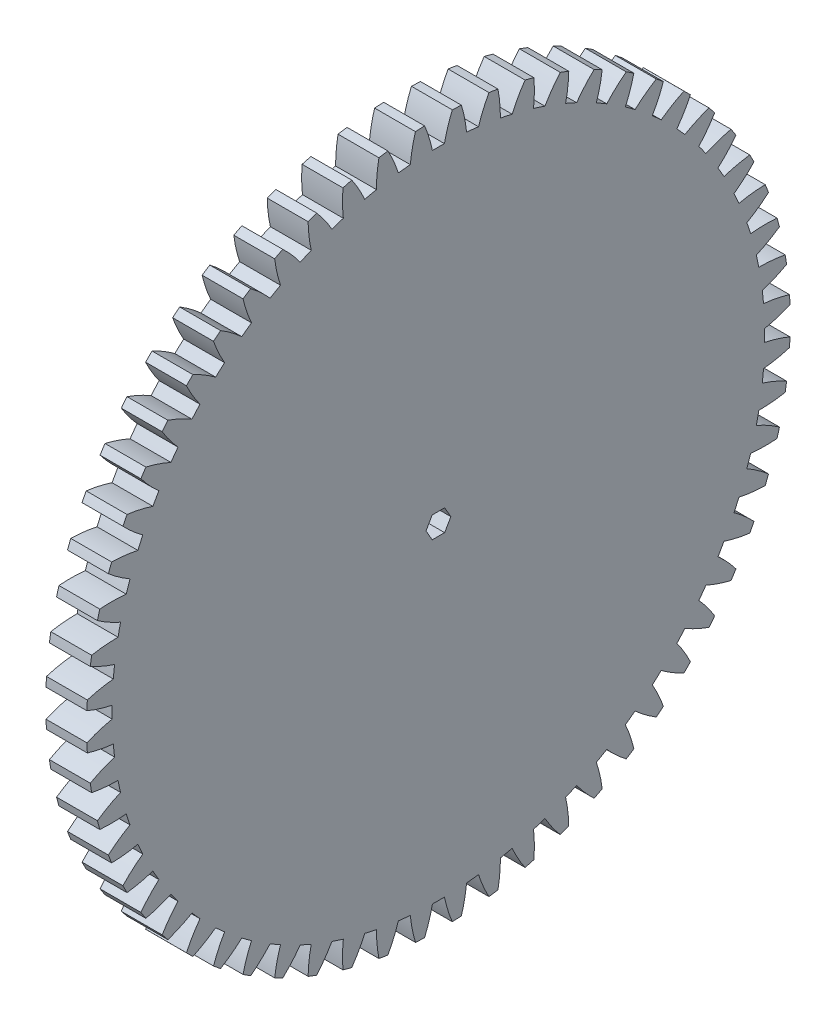
SolidWorks part; units mm, degrees
ref_plane "Plane1" through (0, 0, 0) normal (0, 0, 1) x (1, 0, 0)
ref_plane "Plane2" through (0, 0, 0) normal (0, 1, 0) x (1, 0, 0)
ref_plane "Plane3" through (0, 0, 0) normal (1, 0, 0) x (0, 0, -1)
sketch "HoldingSke" plane through (0, 0, 0) normal (0, 1, 0) x (1, 0, 0)
  line L0 (0, 0) -> (304.8, -527.9291)
  line L1 (-15, 0) -> (100, 0) construction
  line L2 (0, 0) -> (-2.1039, 2.3779)
  line L3 (0, 0) -> (-11.863, 4.5341)
  line L4 (0, 0) -> (4.318, 7.479)
  line L5 (0, 0) -> (-47.5972, -17.7524)
  line L6 (0, 0) -> (-3.1583, -2.1309)
  line L7 (-2.1039, 2.3779) -> (8.8308, 51.9871)
  line L8 (-76.2, 54.61) -> (-61.976, 54.61)
  line L9 (-67.7845, 28.3722) -> (-49.3413, 33.142)
  line L10 (-76.2, 71.12) -> (104.1128, 71.12)
  line L11 (0, 0) -> (-3.81, 0)
  line L12 (-76.2, 101.6) -> (-76.1573, 101.6)
  line L13 (24.9733, 27.94) -> (52.9518, 28.4284)
  line L14 (24.9733, 27.94) -> (25.0241, 27.9398)
  line L15 (24.9733, 27.94) -> (100.4021, 29.52)
  circle A0 centre (0, 0) radius 6.35
  circle A1 centre (0, 0) radius 30.4292
  circle A2 centre (0, 0) radius 38.1
  circle A3 centre (0, 0) radius 6.35
  dimension "MHD" = 60.8584
  dimension "Hub_dia" = 76.2
  dimension "Bore" = 12.7
  dimension "MBD" = 12.7
  dimension "Num_teeth" = 60
  dimension "Pitch" = 609.6
  dimension "Overall_len" = 50.8
  dimension "Show_teeth" = 60
  dimension "Thickness" = 3.81
  dimension "OAL" = 50.8001
  dimension "T_dim" = 14.224
  dimension "Ap" = 14.5
  dimension "H" = 19.05
  dimension "Pitch_radius" = 180.3128
  dimension "Width" = 3.81
  dimension "Backlash" = 0.0427
  dimension "Addendum_fac" = 1
  dimension "Dedendum_fac" = 1.2
  dimension "Clearance_fac" = 0.2
  dimension "Dedendum_add" = 0.0508
sketch "BasProSke" plane through (0, 0, 0) normal (0, 1, 0) x (1, 0, 0)
  line L0 (-10, 0) -> (60, 0) construction
  line L1 (0, 0) -> (0, 32.8083)
  line L2 (0, 0) -> (3.81, 0)
  line L3 (3.81, 0) -> (3.81, 32.8083)
  line L4 (3.81, 32.8083) -> (0, 32.8083)
  dimension "Thickness" = 3.81
  dimension "Diameter" = 65.6167
revolve "Base-Revolve" add sketch "BasProSke" angle 360 about L0
sketch "TooCutSke" plane through (0, 0, 0) normal (1, 0, 0) x (0, 0, -1)
  line L1 (0, 0) -> (0, 107) construction
  line L2 (0, 0) -> (-0.9058, 31.7371) construction
  line L3 (0, 0) -> (-3.3224, 63.395) construction
  line L4 (-0.9058, 31.7371) -> (-1.6612, 31.6975) construction
  arc A0 (0.5605, 30.424) -> (-0.5605, 30.424) centre (0, 0) ccw
  arc A1 (1.3035, 32.8078) -> (-1.3035, 32.8078) centre (0, 0) ccw
  circle A2 centre (0, 0) radius 31.75 construction
  circle A3 centre (0, 0) radius 30.7387 construction
  arc A4 (-0.5605, 30.424) -> (-1.3035, 32.8078) centre (-12.998, 27.8553) ccw
  arc A5 (1.3035, 32.8078) -> (0.5605, 30.424) centre (12.998, 27.8553) ccw
  dimension "Root_dia" = 60.8584
  dimension "Overcut_dia" = 65.6675
  dimension "Pitch_dia" = 63.5
  dimension "Base_dia" = 61.4774
  dimension "Flank_rad" = 12.7
  dimension "Half_ang" = 3
  dimension "Half_CT" = 0.7564
extrude "ToothCut" cut sketch "TooCutSke" along normal through all
fillet "Breaks" [suppressed] radius 0.0212
fillet "RootFillets" [suppressed] radius 0.2625
pattern_circular "TeethCuts" count 60 every 6 about axis through (-10, 0, 0) along (1, 0, 0) of "ToothCut", "RootFillets", "Breaks"
sketch "HubNeaOneSke" plane through (0, 0, 0) normal (-1, 0, 0) x (0, 0, 1)
  circle A0 centre (0, 0) radius 30.4292
  dimension "Diameter" = 60.8584
extrude "HubNearOne" [suppressed] add sketch "HubNeaOneSke" along normal blind 46.9901
sketch "HubNeaBotSke" plane through (0, 0, 0) normal (-1, 0, 0) x (0, 0, 1)
  circle A0 centre (0, 0) radius 30.4292
  dimension "Diameter" = 60.8584
extrude "HubNearBoth" [suppressed] add sketch "HubNeaBotSke" along normal blind 23.495
ref_plane "FarPln" through (3.81, 0, 0) normal (1, 0, 0) x (0, 0, -1)
sketch "HubFarSke" plane through (3.81, 0, 0) normal (1, 0, 0) x (0, 0, -1)
  circle A0 centre (0, 0) radius 30.4292
  dimension "Diameter" = 60.8584
extrude "HubFar" [suppressed] add sketch "HubFarSke" along normal blind 23.495
sketch "BorSke" plane through (0, 0, 0) normal (1, 0, 0) x (0, 0, -1)
  circle A0 centre (0, 0) radius 6.35
  dimension "Diameter" = 12.7
extrude "Bore" cut sketch "BorSke" along normal mid plane 101.6001
sketch "KeySke" plane through (0, 0, 0) normal (1, 0, 0) x (0, 0, -1)
  line L0 (-1.5875, 0) -> (-1.5875, 7.874)
  line L1 (-1.5875, 7.874) -> (1.5875, 7.874)
  line L2 (1.5875, 7.874) -> (1.5875, 0)
  line L3 (0, 0) -> (0, 34) construction
  line L4 (-1.5875, 0) -> (1.5875, 0)
  dimension "Offset" = 7.874
  dimension "Width" = 3.175
extrude "Keyway" [suppressed] cut sketch "KeySke" along normal mid plane 101.6001
pattern_circular "Keyway2" [suppressed] count 2 every 90 about axis through (-10, 0, 0) along (1, 0, 0)
sketch "Sketch1" plane through (3.81, 0, 0) normal (1, 0, 0) x (0, 0, -1)
  circle A0 centre (0, 0) radius 6.35 construction
  circle A1 centre (0, 0) radius 6.35
extrude "Boss-Extrude1" add sketch "Sketch1" against normal blind 7.62
sketch "Sketch2" plane through (-3.81, 0, 0) normal (-1, 0, 0) x (0, 0, 1)
  line L0 (0, 0) -> (7.1354, 0) construction
  line L1 (0, 0) -> (0, 8.2626) construction
  line L3 (1.1585, 0) -> (0.5793, 1.0033)
  line L4 (0.5793, 1.0033) -> (-0.5793, 1.0033)
  line L5 (-0.5793, 1.0033) -> (-1.1585, 0)
  line L6 (-1.1585, 0) -> (-0.5793, -1.0033)
  line L7 (-0.5793, -1.0033) -> (0.5793, -1.0033)
  line L8 (0.5793, -1.0033) -> (1.1585, 0)
  circle A0 centre (0, 0) radius 1.0033 construction
  dimension "D1" = 2.0066
extrude "Cut-Extrude1" cut sketch "Sketch2" against normal through all
equation "' \"Pitch@HoldingSke\" = 4"
equation "' \"Num_teeth@HoldingSke\" = 12"
equation "' \"Ap@HoldingSke\" =  20"
equation "' \"Ap@HoldingSke\" = 20"
equation "' \"Width@HoldingSke\" = 0.5"
equation "' \"Hub_dia@HoldingSke\"= 1"
equation "' \"Hub_dia@HoldingSke\" = 1"
equation "' \"Overall_len@HoldingSke\" = 1.0"
equation "' \"Bore@HoldingSke\" = 0.75"
equation "' \"T_dim@HoldingSke\" = 0.85"
equation "' \"Width@KeySke\" = 0.25"
equation "' \"Show_teeth@HoldingSke\" = 13"
equation "' \"Backlash@HoldingSke\" = 0.009"
equation "' \"Addendum_fac@HoldingSke\" = 1.0"
equation "' \"Dedendum_fac@HoldingSke\" = 1.25"
equation "' \"Dedendum_add@HoldingSke\" = 0.00005"
equation "' \"Clearance_fac@HoldingSke\" = 0.25"
equation "' \"Pitch@HoldingSke\" = 0.5"
equation "' \"Num_teeth@HoldingSke\" = 23"
equation "' \"Show_teeth@HoldingSke\" = 23"
equation "' \"Backlash@HoldingSke\" = 0.0375"
equation "\"Overcut_dia@TooCutSke\" = (\"Num_teeth@HoldingSke\" + 2 * \"Addendum_fac@HoldingSke\") / \"Pitch@HoldingSke\" + 0.002"
equation "\"Pitch_dia@TooCutSke\" = \"Num_teeth@HoldingSke\" / \"Pitch@HoldingSke\""
equation "\"Base_dia@TooCutSke\" = \"Num_teeth@HoldingSke\" / \"Pitch@HoldingSke\" * cos((\"Ap@HoldingSke\"  * 3.14159265 / 180))"
equation "\"Root_dia@TooCutSke\" = (\"Num_teeth@HoldingSke\" + 2) / \"Pitch@HoldingSke\" - 2 * (\"Addendum_fac@HoldingSke\" + \"Dedendum_fac@HoldingSke\") / \"Pitch@HoldingSke\" - \"Dedendum_add@HoldingSke\" * 2"
equation "\"Half_ang@TooCutSke\" = 180 / \"Num_teeth@HoldingSke\""
equation "\"Half_CT@TooCutSke\" = \"Num_teeth@HoldingSke\" / \"Pitch@HoldingSke\" * sin((3.14159265 / 2 / \"Num_teeth@HoldingSke\")) / 2 - 7 * \"Backlash@HoldingSke\" / 4"
equation "\"Flank_rad@TooCutSke\" = \"Num_teeth@HoldingSke\" / \"Pitch@HoldingSke\" / 5"
equation "\"Radius@RootFillets\" = \"Clearance_fac@HoldingSke\" / \"Pitch@HoldingSke\" + \"Dedendum_add@HoldingSke\""
equation "\"Break_rad@Breaks\" = 0.02 / \"Pitch@HoldingSke\""
equation "\"Thickness@HoldingSke\" = \"Width@HoldingSke\""
equation "\"OAL@HoldingSke\" = \"Thickness@HoldingSke\""
equation "\"MHD@HoldingSke\" = (\"Num_teeth@HoldingSke\" + 2) / \"Pitch@HoldingSke\" - 2 * (\"Addendum_fac@HoldingSke\" + \"Dedendum_fac@HoldingSke\")  / \"Pitch@HoldingSke\" - \"Dedendum_add@HoldingSke\" * 2"
equation "\"MBD@HoldingSke\" = (\"Num_teeth@HoldingSke\" + 2) / \"Pitch@HoldingSke\" - 2 * (\"Addendum_fac@HoldingSke\" + \"Dedendum_fac@HoldingSke\")  / \"Pitch@HoldingSke\" - \"Dedendum_add@HoldingSke\" * 2 - 0.002"
equation "\"MHD@HoldingSke\" = ((sgn( \"MHD@HoldingSke\" - \"Hub_dia@HoldingSke\" )-1)*( \"MHD@HoldingSke\" - \"Hub_dia@HoldingSke\" ))/-2+ \"Hub_dia@HoldingSke\""
equation "\"MBD@HoldingSke\" = ((sgn( \"MBD@HoldingSke\" - \"Bore@HoldingSke\" )-1)*( \"MBD@HoldingSke\" - \"Bore@HoldingSke\" ))/-2+ \"Bore@HoldingSke\""
equation "\"OAL@HoldingSke\" = ((sgn( \"OAL@HoldingSke\" - \"Overall_len@HoldingSke\" )+1)*( \"OAL@HoldingSke\" - \"Overall_len@HoldingSke\" ))/2 + \"Overall_len@HoldingSke\" + 0.000002"
equation "\"Num_teeth@TeethCuts\" = int( \"Show_teeth@HoldingSke\" ) + 1"
equation "\"Num_teeth@TeethCuts\" = ((sgn( \"Num_teeth@TeethCuts\" - \"Num_teeth@HoldingSke\" )-1)*( \"Num_teeth@TeethCuts\" - \"Num_teeth@HoldingSke\" ))/-2+ \"Num_teeth@HoldingSke\""
equation "\"Num_teeth@TeethCuts\" = ((sgn( \"Num_teeth@TeethCuts\" - 2.0)+1)*( \"Num_teeth@TeethCuts\" - 2.0))/2 +2.0"
equation "\"Angle@TeethCuts\" = 360.0 / \"Num_teeth@HoldingSke\""
equation "\"Diameter@BasProSke\" = (\"Num_teeth@HoldingSke\" + 2 * \"Addendum_fac@HoldingSke\") / \"Pitch@HoldingSke\""
equation "\"Thickness@BasProSke\"  = \"Thickness@HoldingSke\""
equation "' \"Fillet_rad@BasProSke\" =  \"Thickness@HoldingSke\" * 0.05"
equation "' \"Fillet_rad@BasProSke\" = \"Thickness@HoldingSke\" * 0.05"
equation "\"MHD@HoldingSke\" = ((sgn( \"MHD@HoldingSke\" - \"Root_dia@TooCutSke\" )-1)*( \"MHD@HoldingSke\" - \"Root_dia@TooCutSke\" ))/-2+ \"Root_dia@TooCutSke\""
equation "\"Diameter@HubNeaOneSke\" = \"MHD@HoldingSke\""
equation "\"Length@HubNearOne\" = \"OAL@HoldingSke\" - \"Thickness@BasProSke\""
equation "\"Diameter@HubNeaBotSke\" = \"MHD@HoldingSke\""
equation "\"Length@HubNearBoth\" = ( \"OAL@HoldingSke\" - \"Thickness@BasProSke\" ) / 2.0"
equation "\"Thickness@FarPln\" = \"Thickness@BasProSke\""
equation "\"Diameter@HubFarSke\" = \"MHD@HoldingSke\""
equation "\"Length@HubFar\" = ( \"OAL@HoldingSke\" - \"Thickness@BasProSke\" ) / 2.0"
equation "\"Diameter@BorSke\" = \"MBD@HoldingSke\""
equation "\"D1@Bore\" = \"OAL@HoldingSke\" * 2.0"
equation "\"D1@Keyway\" = \"OAL@HoldingSke\" * 2.0"
equation "\"Offset@KeySke\" = \"T_dim@HoldingSke\" - \"MBD@HoldingSke\" / 2.0"
